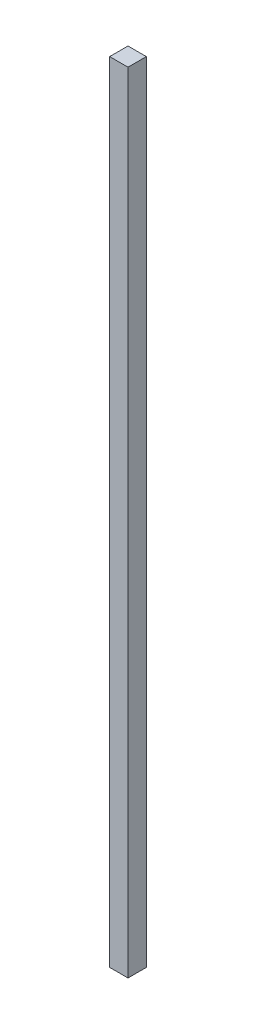
SolidWorks part; units mm, degrees
ref_plane "Front Plane" through (0, 0, 0) normal (0, 0, 1) x (1, 0, 0)
ref_plane "Top Plane" through (0, 0, 0) normal (0, 1, 0) x (1, 0, 0)
ref_plane "Right Plane" through (0, 0, 0) normal (1, 0, 0) x (0, 0, -1)
sketch "Sketch1" plane through (0, 0, 0) normal (0, 1, 0) x (1, 0, 0)
  line L1 (-12.7, -12.7) -> (12.7, -12.7)
  line L2 (-12.7, -12.7) -> (-12.7, 12.7)
  line L3 (-12.7, 12.7) -> (12.7, 12.7)
  line L4 (12.7, -12.7) -> (12.7, 12.7)
  line L5 (-12.7, -12.7) -> (12.7, 12.7) construction
  line L6 (-12.7, 12.7) -> (12.7, -12.7) construction
  point P0 (0, 0)
  dimension "D1" = 25.4
extrude "Boss-Extrude1" add sketch "Sketch1" along normal blind 1092.2 contours L3 L4 L1 L2
